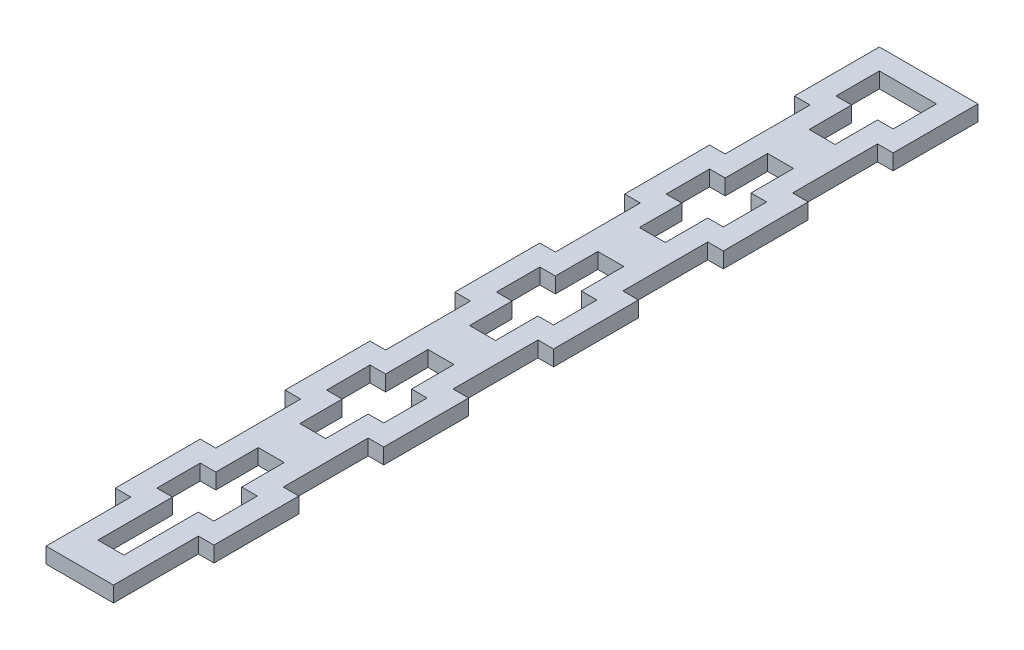
SolidWorks part; units mm, degrees
ref_plane "Front Plane" through (0, 0, 0) normal (0, 0, 1) x (1, 0, 0)
ref_plane "Top Plane" through (0, 0, 0) normal (0, 1, 0) x (1, 0, 0)
ref_plane "Right Plane" through (0, 0, 0) normal (1, 0, 0) x (0, 0, -1)
sketch "Sketch2" plane through (0, 0, 0) normal (0, 1, 0) x (1, 0, 0)
  line L0 (6.5, 98.125) -> (6.5, 81.7708) construction
  line L1 (-9.5, -98.125) -> (9.5, -98.125)
  line L2 (-9.5, -98.125) -> (-9.5, 98.125)
  line L3 (-9.5, 98.125) -> (9.5, 98.125)
  line L4 (9.5, -98.125) -> (9.5, 98.125)
  line L5 (-9.5, -98.125) -> (9.5, 98.125) construction
  line L6 (-9.5, 98.125) -> (9.5, -98.125) construction
  line L7 (6.5, -81.7709) -> (9.5, -81.7709)
  line L8 (6.5, -81.7709) -> (6.5, -98.125)
  line L11 (6.5, -81.7709) -> (9.5, -98.125) construction
  line L12 (6.5, -98.125) -> (9.5, -81.7709) construction
  line L13 (6.5, -49.0625) -> (9.5, -49.0625)
  line L14 (6.5, -49.0625) -> (6.5, -65.4167)
  line L15 (6.5, -65.4167) -> (9.5, -65.4167)
  line L17 (6.5, -49.0625) -> (9.5, -65.4167) construction
  line L18 (6.5, -65.4167) -> (9.5, -49.0625) construction
  line L19 (6.5, -16.3542) -> (9.5, -16.3542)
  line L20 (6.5, -16.3542) -> (6.5, -32.7083)
  line L21 (6.5, -32.7083) -> (9.5, -32.7083)
  line L23 (6.5, -16.3542) -> (9.5, -32.7083) construction
  line L24 (6.5, -32.7083) -> (9.5, -16.3542) construction
  line L25 (6.5, 16.3542) -> (9.5, 16.3542)
  line L26 (6.5, 16.3542) -> (6.5, 0)
  line L27 (6.5, 0) -> (9.5, 0)
  line L29 (6.5, 16.3542) -> (9.5, 0) construction
  line L30 (6.5, 0) -> (9.5, 16.3542) construction
  line L31 (6.5, 49.0625) -> (9.5, 49.0625)
  line L32 (6.5, 49.0625) -> (6.5, 32.7083)
  line L33 (6.5, 32.7083) -> (9.5, 32.7083)
  line L35 (6.5, 49.0625) -> (9.5, 32.7083) construction
  line L36 (6.5, 32.7083) -> (9.5, 49.0625) construction
  line L37 (6.5, 81.7708) -> (9.5, 81.7708)
  line L38 (6.5, 81.7708) -> (6.5, 65.4167)
  line L39 (6.5, 65.4167) -> (9.5, 65.4167)
  line L41 (6.5, 81.7708) -> (9.5, 65.4167) construction
  line L42 (6.5, 65.4167) -> (9.5, 81.7708) construction
  line L43 (6.5, 65.4167) -> (6.5, 49.0625) construction
  line L44 (6.5, 32.7083) -> (6.5, 16.3542) construction
  line L45 (6.5, 0) -> (6.5, -16.3542) construction
  line L46 (6.5, -32.7083) -> (6.5, -49.0625) construction
  line L47 (6.5, -65.4167) -> (6.5, -81.7709) construction
  line L48 (0, -98.125) -> (0, 98.125) construction
  line L51 (-6.5, -81.7709) -> (-9.5, -81.7709)
  line L52 (-6.5, -81.7709) -> (-6.5, -98.125)
  line L53 (-6.5, -65.4167) -> (-9.5, -65.4167)
  line L55 (-6.5, -49.0625) -> (-9.5, -49.0625)
  line L56 (-6.5, -49.0625) -> (-6.5, -65.4167)
  line L57 (-6.5, -32.7083) -> (-9.5, -32.7083)
  line L59 (-6.5, -16.3542) -> (-9.5, -16.3542)
  line L60 (-6.5, -16.3542) -> (-6.5, -32.7083)
  line L61 (-6.5, 0) -> (-9.5, 0)
  line L63 (-6.5, 16.3542) -> (-9.5, 16.3542)
  line L64 (-6.5, 16.3542) -> (-6.5, 0)
  line L65 (-6.5, 32.7083) -> (-9.5, 32.7083)
  line L67 (-6.5, 49.0625) -> (-9.5, 49.0625)
  line L68 (-6.5, 49.0625) -> (-6.5, 32.7083)
  line L69 (-6.5, 65.4167) -> (-9.5, 65.4167)
  line L71 (-6.5, 81.7708) -> (-9.5, 81.7708)
  line L72 (-6.5, 81.7708) -> (-6.5, 65.4167)
  line L73 (-6.5, 65.4167) -> (6.5, 65.4167)
  point P0 (0, 0)
  point P6 (8, -89.9479)
  point P7 (8, -57.2396)
  point P15 (8, -24.5313)
  point P20 (8, 8.1771)
  point P25 (8, 40.8854)
  point P30 (8, 73.5938)
  dimension "D1" = 19
  dimension "D2" = 163.5417
  dimension "D3" = 3
extrude "Boss-Extrude1" add sketch "Sketch2" along normal blind 3 contours L71 L72 L69 L2 L67 L68 L65 L63 L64 L61 L59 L60 L57 L55 L56 L53 L51 L52 L1 L8 L7 L4 L15 L14 L13 L21 L20 L19 L27 L26 L25 L33 L32 L31 L39 L38 L37 L3
sketch "Sketch3" plane through (0, 3, 0) normal (0, 1, 0) x (1, 0, 0)
  line L0 (-2.5, 36.8854) -> (2.5, 36.8854)
  line L1 (2.5, 36.8854) -> (2.5, 28.7083)
  line L2 (2.5, 28.7083) -> (5.5, 28.7083)
  line L3 (5.5, 28.7083) -> (5.5, 20.3542)
  line L4 (5.5, 20.3542) -> (2.5, 20.3542)
  line L5 (2.5, 20.3542) -> (2.5, 12.1771)
  line L6 (2.5, 12.1771) -> (-2.5, 12.1771)
  line L7 (-2.5, 12.1771) -> (-2.5, 20.3542)
  line L8 (-2.5, 20.3542) -> (-5.5, 20.3542)
  line L9 (-5.5, 20.3542) -> (-5.5, 28.7083)
  line L10 (-5.5, 28.7083) -> (-2.5, 28.7083)
  line L11 (-2.5, 28.7083) -> (-2.5, 36.8854)
  line L12 (5.5, 24.5313) -> (9.5, 24.5313) construction
  line L13 (9.5, 16.3542) -> (9.5, 32.7083) construction
  line L14 (2.5, 36.8854) -> (6.5, 36.8854) construction
  line L15 (6.5, 49.0625) -> (6.5, 32.7083) construction
  line L16 (8, 32.7083) -> (8, 28.7083) construction
  line L17 (6.5, 32.7083) -> (9.5, 32.7083) construction
  line L18 (0, 36.8854) -> (0, 40.8854) construction
  line L19 (-2.5, -4) -> (-2.5, 4.1771)
  line L20 (-2.5, 4.1771) -> (2.5, 4.1771)
  line L21 (2.5, 4.1771) -> (2.5, -4)
  line L22 (2.5, -4) -> (5.5, -4)
  line L23 (5.5, -4) -> (5.5, -12.3542)
  line L24 (5.5, -12.3542) -> (2.5, -12.3542)
  line L25 (2.5, -12.3542) -> (2.5, -20.5313)
  line L26 (2.5, -20.5313) -> (-2.5, -20.5313)
  line L27 (-2.5, -20.5313) -> (-2.5, -12.3542)
  line L28 (-2.5, -12.3542) -> (-5.5, -12.3542)
  line L29 (-5.5, -12.3542) -> (-5.5, -4)
  line L30 (-5.5, -4) -> (-2.5, -4)
  line L31 (-2.5, -36.7083) -> (-2.5, -28.5313)
  line L32 (-2.5, -28.5313) -> (2.5, -28.5313)
  line L33 (2.5, -28.5313) -> (2.5, -36.7083)
  line L34 (2.5, -36.7083) -> (5.5, -36.7083)
  line L35 (5.5, -36.7083) -> (5.5, -45.0625)
  line L36 (5.5, -45.0625) -> (2.5, -45.0625)
  line L37 (2.5, -45.0625) -> (2.5, -53.2396)
  line L38 (2.5, -53.2396) -> (-2.5, -53.2396)
  line L39 (-2.5, -53.2396) -> (-2.5, -45.0625)
  line L40 (-2.5, -45.0625) -> (-5.5, -45.0625)
  line L41 (-5.5, -45.0625) -> (-5.5, -36.7083)
  line L42 (-5.5, -36.7083) -> (-2.5, -36.7083)
  line L43 (-2.5, -69.4167) -> (-2.5, -61.2396)
  line L44 (-2.5, -61.2396) -> (2.5, -61.2396)
  line L45 (2.5, -61.2396) -> (2.5, -69.4167)
  line L46 (2.5, -69.4167) -> (5.5, -69.4167)
  line L47 (5.5, -69.4167) -> (5.5, -77.7708)
  line L48 (5.5, -77.7708) -> (2.5, -77.7708)
  line L49 (2.5, -77.7708) -> (2.5, -85.9479)
  line L50 (2.5, -85.9479) -> (-2.5, -85.9479)
  line L51 (-2.5, -85.9479) -> (-2.5, -77.7708)
  line L52 (-2.5, -77.7708) -> (-5.5, -77.7708)
  line L53 (-5.5, -77.7708) -> (-5.5, -69.4167)
  line L54 (-5.5, -69.4167) -> (-2.5, -69.4167)
  line L55 (9.5, -16.3542) -> (9.5, 0) construction
  line L56 (-2.5, -85.9479) -> (-2.5, -92.125)
  line L57 (-2.5, -92.125) -> (2.5, -92.125)
  line L58 (2.5, -92.125) -> (2.5, -85.9479)
  line L59 (-6.5, -98.125) -> (6.5, -98.125) construction
  line L60 (-5.5, 61.4167) -> (5.5, 61.4167)
  line L61 (5.5, 61.4167) -> (5.5, 53.0625)
  line L62 (5.5, 53.0625) -> (2.5, 53.0625)
  line L63 (2.5, 53.0625) -> (2.5, 44.8854)
  line L64 (2.5, 44.8854) -> (-2.5, 44.8854)
  line L65 (-2.5, 44.8854) -> (-2.5, 53.0625)
  line L66 (-2.5, 53.0625) -> (-5.5, 53.0625)
  line L67 (-5.5, 53.0625) -> (-5.5, 61.4167)
  line L68 (5.5, 65.4167) -> (5.5, 61.4167) construction
  line L69 (-9.5, 65.4167) -> (9.5, 65.4167) construction
  line L70 (9.5, 61.4167) -> (5.5, 61.4167) construction
  line L71 (9.5, 49.0625) -> (9.5, 65.4167) construction
  line L72 (2.5, 44.8854) -> (6.5, 44.8854) construction
  line L73 (0, 40.8854) -> (0, 44.8854) construction
  line L74 (8, 49.0625) -> (8, 53.0625) construction
  line L75 (6.5, 49.0625) -> (9.5, 49.0625) construction
  point P2 (0, 12.1771)
  point P18 (9.5, 24.5313)
  point P28 (6.5, 40.8854)
  point P29 (5.5, -8.1771)
  point P68 (9.5, -8.1771)
  point P82 (0, 61.4167)
  dimension "D1" = 4
  dimension "D3" = 6
  dimension "D2" = 4
extrude "Cut-Extrude1" cut sketch "Sketch3" against normal through all both and the other way through all contours L67 L66 L65 L64 L63 L62 L61 L60 | L11 L10 L9 L8 L7 L6 L5 L4 L3 L2 L1 L0 | L30 L29 L28 L27 L26 L25 L24 L23 L22 L21 L20 L19 | L54 L53 L52 L51 L50 L49 L48 L47 L46 L45 L44 L43 | L57 L58 L50 L56 | L42 L41 L40 L39 L38 L37 L36 L35 L34 L33 L32 L31
